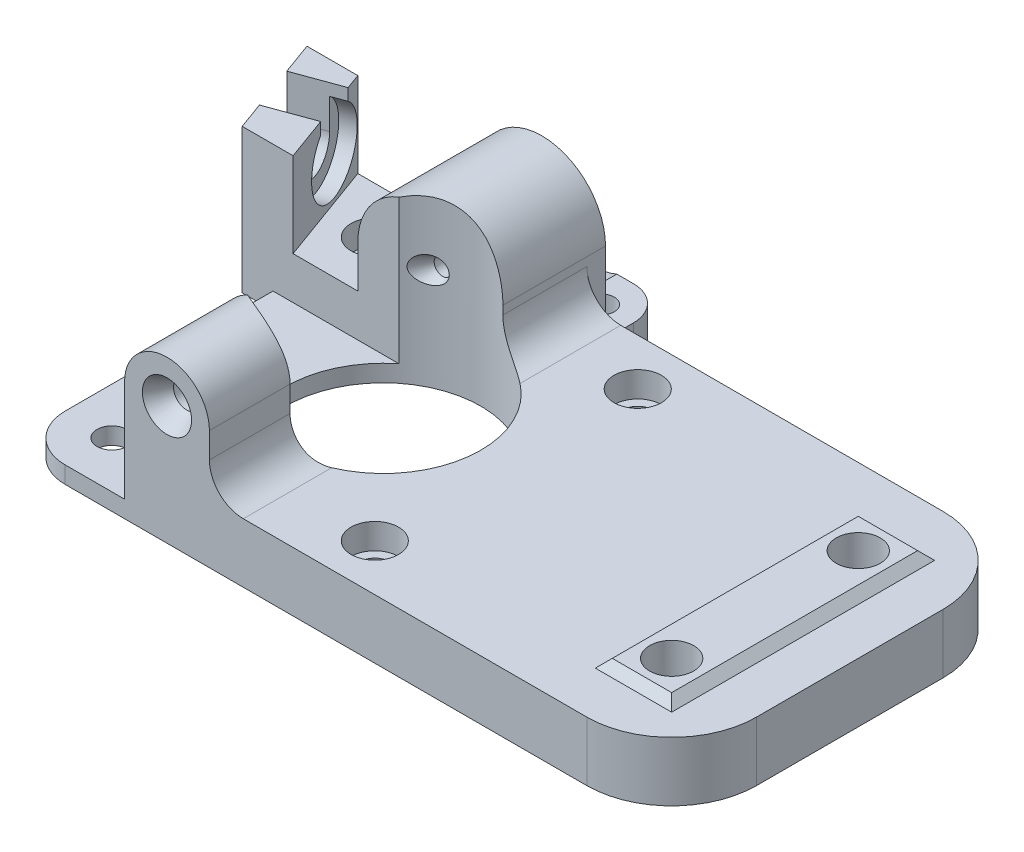
SolidWorks part; units mm, degrees
ref_plane "Front Plane" through (0, 0, 0) normal (0, 0, 1) x (1, 0, 0)
ref_plane "Top Plane" through (0, 0, 0) normal (0, 1, 0) x (1, 0, 0)
ref_plane "Right Plane" through (0, 0, 0) normal (1, 0, 0) x (0, 0, -1)
sketch "Sketch1" plane through (0, 0, 0) normal (0, 1, 0) x (1, 0, 0)
  line L0 (0, 0) -> (0, 42)
  line L1 (0, 0) -> (77, 0)
  line L2 (0, 42) -> (77, 42)
  line L3 (77, 0) -> (77, 42)
  dimension "D1" = 77
  dimension "D2" = 42
extrude "Boss-Extrude1" add sketch "Sketch1" along normal blind 7
fillet "Fillet1" radius 10 1 edges at (77, 3.5, 0)
fillet "Fillet2" radius 10 1 edges at (77, 3.5, -42)
fillet "Fillet3" radius 5.5 1 edges at (0, 3.5, 0)
sketch "Sketch2" plane through (0, 7, 0) normal (0, 1, 0) x (1, 0, 0)
  line L0 (71.5, 5.5) -> (62.5, 5.5)
  line L1 (71.5, 5.5) -> (71.5, 36.5)
  line L2 (62.5, 5.5) -> (62.5, 36.5)
  line L3 (71.5, 36.5) -> (62.5, 36.5)
  line L4 (5.5, 0) -> (67, 0) construction
  line L5 (77, 10) -> (77, 32) construction
  dimension "D1" = 5.5
  dimension "D2" = 5.5
  dimension "D3" = 31
  dimension "D4" = 9
extrude "Boss-Extrude2" add sketch "Sketch2" along normal blind 1
sketch "Sketch3" plane through (71.5, 0, 0) normal (1, 0, 0) x (0, 0, -1)
  line L0 (5.5, 7) -> (5.5, 8)
  line L1 (5.5, 8) -> (6.5, 8)
  line L2 (5.5, 8) -> (36.5, 8) construction
  line L3 (6.5, 8) -> (5.5, 7)
  dimension "D1" = 1
extrude "Cut-Extrude1" cut sketch "Sketch3" against normal blind 11
ref_plane "Plane1" through (0, 0, -21) normal (0, 0, 1) x (1, 0, 0)
sketch "Sketch4" plane through (0, 0, -36.5) normal (0, 0, -1) x (-1, 0, 0)
  line L0 (-71.5, 8) -> (-70.5, 8)
  line L1 (-71.5, 8) -> (-62.5, 8) construction
  line L2 (-70.5, 8) -> (-71.5, 7)
  line L3 (-71.5, 7) -> (-71.5, 8)
  line L4 (-62.5, 8) -> (-62.5, 7)
  line L5 (-62.5, 7) -> (-63.5, 8)
  line L6 (-63.5, 8) -> (-62.5, 8)
  dimension "D1" = 1
  dimension "D2" = 1
extrude "Cut-Extrude2" cut sketch "Sketch4" against normal blind 31
mirror "Mirror2" about plane through (0, 0, -21) normal (0, 0, 1) of "Cut-Extrude1"
sketch "Sketch5" plane through (0, 8, 0) normal (0, 1, 0) x (1, 0, 0)
  line L0 (63.5, 6.5) -> (63.5, 35.5) construction
  line L1 (70.5, 6.5) -> (63.5, 6.5) construction
  circle A0 centre (67, 10) radius 2.6
  dimension "D1" = 5.2
  dimension "D2" = 3.5
  dimension "D3" = 3.5
extrude "Cut-Extrude3" cut sketch "Sketch5" against normal blind 6
mirror "Mirror3" about plane through (0, 0, -21) normal (0, 0, 1) of "Cut-Extrude3"
sketch "Sketch6" plane through (0, 7, 0) normal (0, 1, 0) x (1, 0, 0)
  line L0 (5.5, 0) -> (67, 0) construction
  line L1 (77, 10) -> (77, 32) construction
  circle A0 centre (36.5, 5.5) radius 2.8
  dimension "D1" = 5.6
  dimension "D2" = 5.5
  dimension "D3" = 40.5
extrude "Cut-Extrude4" cut sketch "Sketch6" against normal blind 3
sketch "Sketch7" plane through (0, 4, 0) normal (0, 1, 0) x (1, 0, 0)
  circle A0 centre (36.5, 5.5) radius 1.75
  dimension "D1" = 3.5
extrude "Cut-Extrude5" cut sketch "Sketch7" against normal blind 4
mirror "Mirror4" about plane through (0, 0, -21) normal (0, 0, 1) of "Cut-Extrude4", "Cut-Extrude5"
sketch "Sketch8" plane through (0, 7, 0) normal (0, 1, 0) x (1, 0, 0)
  line L0 (14.5, 0) -> (14.5, 30)
  line L1 (14.5, 0) -> (0, 0)
  line L2 (14.5, 30) -> (0, 30)
  line L3 (0, 0) -> (0, 30)
  line L4 (5.5, 0) -> (67, 0) construction
  line L8 (0, 42) -> (0, 5.5) construction
  dimension "D1" = 30
  dimension "D2" = 14.5
extrude "Cut-Extrude6" cut sketch "Sketch8" against normal blind 5
sketch "Sketch9" plane through (0, 0, 0) normal (0, 0, 1) x (1, 0, 0)
  line L0 (12.5, 2) -> (12.5, 14)
  line L1 (5.5, 2) -> (14.5, 2) construction
  line L2 (22.5, 14) -> (22.5, 7)
  line L3 (14.5, 7) -> (67, 7) construction
  line L4 (22.5, 7) -> (14.5, 7)
  line L5 (14.5, 7) -> (14.5, 2)
  line L6 (14.5, 2) -> (12.5, 2)
  arc A0 (22.5, 14) -> (12.5, 14) centre (17.5, 14) ccw
  dimension "D3" = 10
  dimension "D1" = 12.5
  dimension "D2" = 12
  dimension "D4" = 7
extrude "Boss-Extrude3" add sketch "Sketch9" against normal blind 11.5
sketch "Sketch10" plane through (0, 0, 0) normal (0, -1, 0) x (1, 0, 0)
  line L0 (26.5, -42) -> (26.5, -46)
  line L1 (67, -42) -> (0, -42) construction
  line L2 (22.5, -50) -> (12.5, -50)
  line L3 (8.5, -46) -> (8.5, -42)
  line L4 (26.5, -42) -> (8.5, -42)
  line L6 (77, -10) -> (77, -32) construction
  arc A0 (26.5, -46) -> (22.5, -50) centre (22.5, -46) cw
  arc A1 (12.5, -50) -> (8.5, -46) centre (12.5, -46) cw
  point P9 (26.5, -44)
  dimension "D2" = 4
  dimension "D3" = 4
  dimension "D1" = 8
  dimension "D4" = 18
  dimension "D5" = 50.5
extrude "Boss-Extrude4" add sketch "Sketch10" against normal blind 4
ref_plane "Plane2" through (0, 0, -44.2) normal (0, 0, -1) x (-1, 0, 0)
sketch "Sketch11" plane through (0, 0, -44.2) normal (0, 0, -1) x (-1, 0, 0)
  line L0 (-25, 4) -> (-25, 12)
  line L1 (-10, 12) -> (-10, 4)
  line L2 (-10, 4) -> (-25, 4)
  line L3 (-12.5, 4) -> (-22.5, 4) construction
  line L4 (-26.5, 4) -> (-26.5, 0) construction
  arc A0 (-25, 12) -> (-10, 12) centre (-17.5, 12) cw
  point P10 (-26.5, 2)
  dimension "D1" = 7.5
  dimension "D2" = 1.5
  dimension "D3" = 8
extrude "Boss-Extrude5" add sketch "Sketch11" against normal blind 14.2
fillet "Fillet4" radius 4 1 edges at (22.5, 7, -5.75)
fillet "Fillet5" radius 4 1 edges at (25, 7, -36)
sketch "Sketch12" plane through (0, 7, 0) normal (0, 1, 0) x (1, 0, 0)
  line L0 (10, 42) -> (0, 42) construction
  line L1 (0, 30) -> (0, 5.5) construction
  circle A0 centre (22, 21) radius 11.5
  dimension "D1" = 23
  dimension "D2" = 21
  dimension "D3" = 22
extrude "Cut-Extrude7" cut sketch "Sketch12" against normal blind 14 and the other way blind 14
sketch "Sketch13" plane through (0, 2, 0) normal (0, 1, 0) x (1, 0, 0)
  line L0 (11.6306, 11.5) -> (11.6306, 30)
  line L1 (11.6306, 11.5) -> (17.8159, 11.5)
  line L2 (11.6306, 30) -> (17.8159, 30)
  line L3 (17.8159, 11.5) -> (17.8159, 30)
  line L4 (14.5, 30) -> (0, 30) construction
  line L5 (12.5, 11.5) -> (14.5, 11.5) construction
extrude "Cut-Extrude8" cut sketch "Sketch13" along normal blind 14
sketch "Sketch14" plane through (0, 7, 0) normal (0, 1, 0) x (1, 0, 0)
  line L0 (10, 42) -> (-8, 42)
  line L1 (-8, 42) -> (-3.6324, 30)
  line L2 (-3.6324, 30) -> (10, 30)
  line L3 (10, 30) -> (10, 42)
  dimension "D1" = 18
  dimension "D2" = 70
extrude "Boss-Extrude6" add sketch "Sketch14" along normal blind 10 and the other way blind 7
sketch "Sketch15" plane through (0, 17, 0) normal (0, 1, 0) x (1, 0, 0)
  line L0 (10, 42) -> (10, 30)
  line L1 (10, 30) -> (2.3676, 30)
  line L2 (2.3676, 30) -> (-2, 42)
  line L4 (-2, 42) -> (10, 42)
  dimension "D1" = 12
  dimension "D2" = 70
extrude "Cut-Extrude9" cut sketch "Sketch15" against normal blind 10
sketch "Sketch16" plane through (0, 0, -44.2) normal (0, 0, -1) x (-1, 0, 0)
  line L0 (-10, 4) -> (-10, 12) construction
  line L1 (-25, 4) -> (-10, 4) construction
  circle A0 centre (-17.5, 12) radius 4.85
  dimension "D1" = 9.7
  dimension "D2" = 7.5
  dimension "D3" = 8
extrude "Cut-Extrude10" cut sketch "Sketch16" against normal blind 10
sketch "Sketch17" plane through (0, 0, -34.2) normal (0, 0, -1) x (-1, 0, 0)
  circle A0 centre (-17.5, 12) radius 1
  dimension "D1" = 2
extrude "Cut-Extrude11" cut sketch "Sketch17" against normal blind 5
sketch "Sketch19" plane through (0, 7, 0) normal (0, 1, 0) x (1, 0, 0)
  line L0 (10, 42) -> (-2, 42) construction
  line L1 (10, 30) -> (10, 42) construction
  circle A0 centre (5.5, 36.5) radius 2.8
  dimension "D1" = 5.6
  dimension "D2" = 5.5
  dimension "D3" = 4.5
extrude "Cut-Extrude12" cut sketch "Sketch19" against normal blind 3
sketch "Sketch20" plane through (0, 4, 0) normal (0, 1, 0) x (1, 0, 0)
  circle A0 centre (5.5, 36.5) radius 1.75
  dimension "D1" = 3.5
extrude "Cut-Extrude13" cut sketch "Sketch20" against normal blind 8
sketch "Sketch21" plane through (11.7325, 0, -4.2703) normal (0.9397, 0, -0.342) x (-0.342, 0, -0.9397)
  line L1 (27.381, 7) -> (27.381, 17) construction
  line L2 (40.1511, 7) -> (27.381, 7) construction
  circle A0 centre (35.531, 12) radius 4.5
  dimension "D1" = 9
  dimension "D2" = 8.15
  dimension "D3" = 5
extrude "Cut-Extrude14" cut sketch "Sketch21" against normal blind 1.7
sketch "Sketch22" plane through (10.135, 0, -3.6888) normal (0.9397, 0, -0.342) x (-0.342, 0, -0.9397)
  line L0 (32.831, 12) -> (32.831, 17)
  line L1 (32.831, 17) -> (38.231, 17)
  line L2 (38.231, 17) -> (38.231, 12)
  arc A0 (32.831, 12) -> (38.231, 12) centre (35.531, 12) ccw
  dimension "D1" = 5.4
extrude "Cut-Extrude15" cut sketch "Sketch22" against normal blind 31.7 and the other way blind 1.7
sketch "Sketch23" plane through (0, 2, 0) normal (0, 1, 0) x (1, 0, 0)
  line L0 (5.5, 0) -> (12.5, 0) construction
  line L1 (0, 30) -> (0, 5.5) construction
  circle A0 centre (5.5, 5.5) radius 1.75
  point P4 (9, 0)
  dimension "D1" = 3.5
  dimension "D2" = 5.5
  dimension "D3" = 5.5
extrude "Cut-Extrude16" cut sketch "Sketch23" against normal blind 50.7
sketch "Sketch24" plane through (0, 0, 0) normal (0, 0, 1) x (1, 0, 0)
  circle A0 centre (17.5, 14) radius 2.9
  dimension "D1" = 5.8
extrude "Cut-Extrude17" cut sketch "Sketch24" against normal blind 2.325 draft 30
sketch "Sketch25" plane through (0, 0, -2.325) normal (0, 0, 1) x (1, 0, 0)
  circle A0 centre (17.5, 14) radius 1.5577
extrude "Cut-Extrude18" cut sketch "Sketch25" against normal up to next
sketch "Sketch26" plane through (0, 0, -50) normal (0, 0, -1) x (-1, 0, 0)
  line L1 (-25, 4) -> (-10, 4) construction
  circle A0 centre (-17.6999, 10.4) radius 7
  dimension "D1" = 14
  dimension "D2" = 6.4
extrude "Cut-Extrude19" cut sketch "Sketch26" against normal up to surface (5.8 mm away) up to face at (12.65, 12, -44.2)
sketch "Sketch27" plane through (0, 4, 0) normal (0, 1, 0) x (1, 0, 0)
  line L0 (20.5354, 50) -> (22.5, 50) construction
  line L1 (12.5, 50) -> (14.8645, 50) construction
  line L2 (20.5354, 44.2) -> (20.5354, 50) construction
  line L3 (14.8645, 50) -> (14.8645, 44.2) construction
  circle A0 centre (22.7354, 46) radius 1.5
  circle A1 centre (12.6645, 46) radius 1.5
  dimension "D1" = 3
  dimension "D2" = 3
  dimension "D3" = 4
  dimension "D4" = 4
  dimension "D5" = 2.2
  dimension "D6" = 2.2
extrude "Cut-Extrude20" cut sketch "Sketch27" against normal through all
sketch "Sketch29" plane through (0, 0, 0) normal (0, -1, 0) x (-1, 0, 0)
  line L1 (-77, 10) -> (-77, 32) construction
  line L2 (-67, 42) -> (-26.5, 42) construction
  circle A0 centre (-67, 32) radius 5
  dimension "D1" = 10
  dimension "D2" = 10
  dimension "D3" = 10
extrude "Cut-Extrude21" cut sketch "Sketch29" against normal blind 2
mirror "Mirror5" about plane through (0, 0, -21) normal (0, 0, 1) of "Mirror3", "Cut-Extrude21"
ref_plane "Plane3" through (0, 0, -30) normal (0, 0, 1) x (1, 0, 0)
sketch "Sketch30" plane through (0, 0, -30) normal (0, 0, 1) x (1, 0, 0)
  circle A0 centre (17.5, 12) radius 2.3
  dimension "D1" = 4.6
ref_plane "Plane4" through (0, 0, -32.5) normal (0, 0, 1) x (1, 0, 0)
sketch "Sketch35" plane through (0, 0, -32.5) normal (0, 0, 1) x (1, 0, 0)
  circle A0 centre (17.5, 12) radius 1
extrude "Cut-Extrude23" cut sketch "Sketch35" along normal blind 2.3 draft 28 draft outward yes
